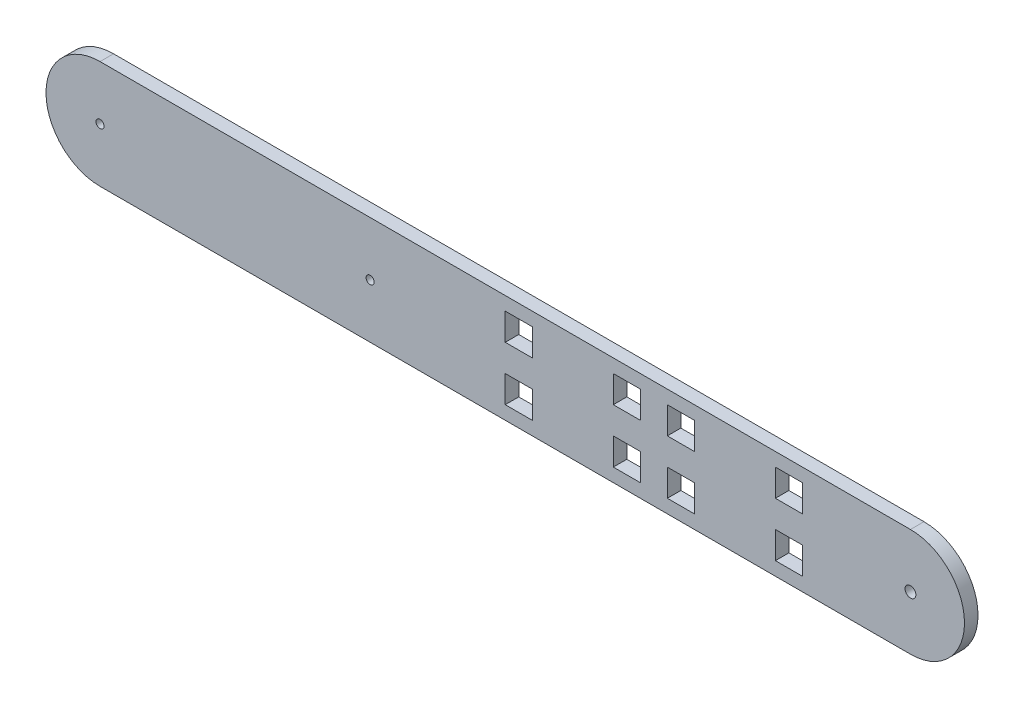
SolidWorks part; units mm, degrees
ref_plane "Front Plane" through (0, 0, 0) normal (0, 0, 1) x (1, 0, 0)
ref_plane "Top Plane" through (0, 0, 0) normal (0, 1, 0) x (1, 0, 0)
ref_plane "Right Plane" through (0, 0, 0) normal (1, 0, 0) x (0, 0, -1)
sketch "Sketch1" plane through (0, 0, 0) normal (0, 0, 1) x (1, 0, 0)
  line L0 (-126.9044, 0) -> (173.0956, 0) construction
  line L1 (-126.9044, 20) -> (173.0956, 20)
  line L2 (-126.9044, -20) -> (173.0956, -20)
  line L3 (173.0956, 15) -> (-126.9044, 15) construction
  line L4 (173.0956, 10) -> (-126.9044, 10) construction
  line L5 (-126.9044, -15) -> (173.0956, -15) construction
  line L6 (173.0956, -10) -> (-126.9044, -10) construction
  line L7 (-126.9044, -5) -> (173.0956, -5) construction
  line L8 (173.0956, 5) -> (-126.9044, 5) construction
  line L9 (23.0956, -20) -> (23.0956, 20) construction
  line L10 (-57.7377, 20) -> (-57.7377, -20) construction
  line L12 (23.0956, 15) -> (23.0956, 10)
  line L15 (63.0956, 15) -> (73.0956, 15)
  line L16 (63.0956, 15) -> (63.0956, 10)
  line L18 (73.0956, 15) -> (73.0956, 10)
  line L20 (83.0956, 10) -> (83.0956, 5)
  line L21 (83.0956, 5) -> (93.0956, 5)
  line L22 (93.0956, 10) -> (93.0956, 5)
  line L24 (123.0956, 10) -> (123.0956, 5)
  line L25 (123.0956, 5) -> (133.0956, 5)
  line L26 (133.0956, 10) -> (133.0956, 5)
  line L27 (33.0956, -15) -> (23.0956, -15)
  line L28 (33.0956, -15) -> (33.0956, -10)
  line L30 (23.0956, -15) -> (23.0956, -10)
  line L31 (63.0956, -15) -> (73.0956, -15)
  line L32 (63.0956, -15) -> (63.0956, -10)
  line L34 (73.0956, -15) -> (73.0956, -10)
  line L36 (83.0956, -10) -> (83.0956, -5)
  line L37 (83.0956, -5) -> (93.0956, -5)
  line L38 (93.0956, -10) -> (93.0956, -5)
  line L39 (123.0956, -5) -> (133.0956, -5)
  line L40 (123.0956, -5) -> (123.0956, -10)
  line L42 (133.0956, -5) -> (133.0956, -10)
  line L43 (63.0956, 10) -> (63.0956, 5)
  line L44 (23.0956, 15) -> (33.0956, 15)
  line L45 (23.0956, 15) -> (23.0956, 5)
  line L46 (23.0956, 5) -> (33.0956, 5)
  line L47 (33.0956, 15) -> (33.0956, 5)
  line L48 (63.0956, 5) -> (73.0956, 5)
  line L49 (73.0956, 5) -> (73.0956, 10)
  line L50 (63.0956, -10) -> (63.0956, -5)
  line L51 (63.0956, -5) -> (73.0956, -5)
  line L52 (73.0956, -5) -> (73.0956, -10)
  line L53 (23.0956, -10) -> (23.0956, -5)
  line L54 (23.0956, -5) -> (33.0956, -5)
  line L55 (33.0956, -5) -> (33.0956, -10)
  line L56 (83.0956, 10) -> (83.0956, 15)
  line L57 (83.0956, 15) -> (93.0956, 15)
  line L58 (93.0956, 15) -> (93.0956, 10)
  line L59 (83.0956, -10) -> (83.0956, -15)
  line L60 (83.0956, -15) -> (93.0956, -15)
  line L61 (93.0956, -15) -> (93.0956, -10)
  line L62 (123.0956, -10) -> (123.0956, -15)
  line L63 (123.0956, -15) -> (133.0956, -15)
  line L64 (133.0956, -15) -> (133.0956, -10)
  line L65 (123.0956, 10) -> (123.0956, 15)
  line L66 (123.0956, 15) -> (133.0956, 15)
  line L67 (133.0956, 15) -> (133.0956, 10)
  arc A0 (-126.9044, 20) -> (-126.9044, -20) centre (-126.9044, 0) ccw
  arc A1 (173.0956, -20) -> (173.0956, 20) centre (173.0956, 0) ccw
  circle A2 centre (-126.9044, 0) radius 1.5
  circle A3 centre (173.0956, 0) radius 2
  circle A5 centre (-26.9044, 0) radius 1.5
  point P3 (23.0956, 0)
  dimension "D3" = 3
  dimension "D4" = 4
  dimension "D22" = 3
  dimension "D23" = 100
  dimension "D1" = 300
  dimension "D2" = 40
  dimension "D5" = 5
  dimension "D6" = 5
  dimension "D7" = 5
  dimension "D8" = 10
  dimension "D9" = 5
  dimension "D10" = 5
  dimension "D11" = 150
  dimension "D13" = 10
  dimension "D15" = 10
  dimension "D16" = 10
  dimension "D17" = 30
  dimension "D18" = 10
  dimension "D19" = 10
  dimension "D20" = 10
  dimension "D21" = 30
extrude "Boss-Extrude1" add sketch "Sketch1" along normal blind 5 contours L2 A1 L1 A0 A5 A3 A2 L66 L67 L26 L25 L24 L65 L57 L58 L22 L21 L20 L56 L54 L55 L28 L27 L30 L53 L51 L52 L34 L31 L32 L50 L44 L47 L46 L45 L12 L49 L48 L43 L16 L15 L18
